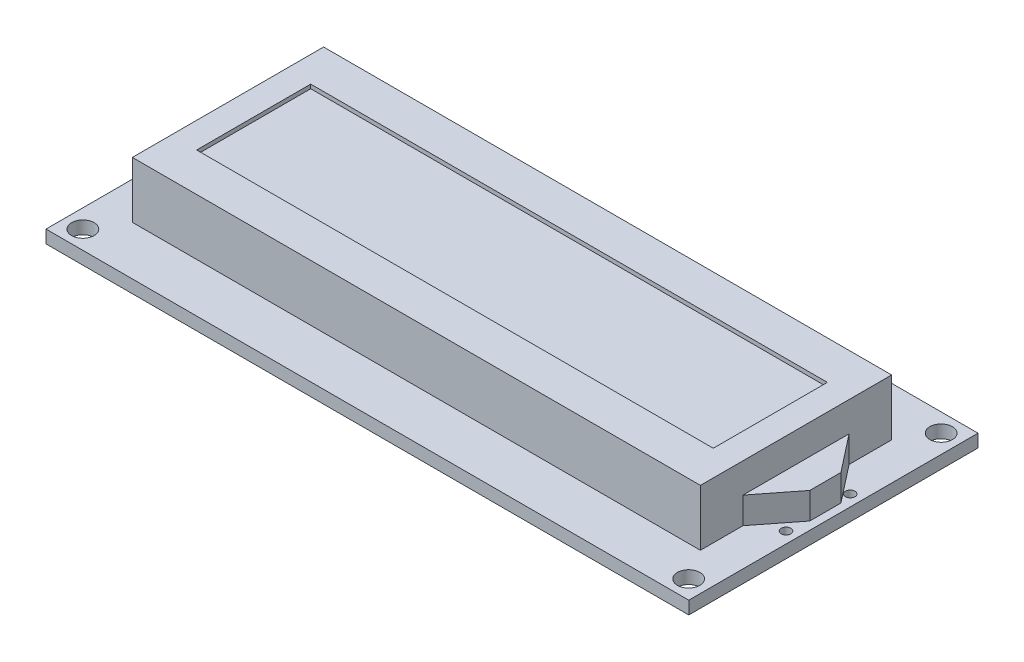
SolidWorks part; units mm, degrees
ref_plane "Front" through (0, 0, 0) normal (0, 0, 1) x (1, 0, 0)
ref_plane "Top" through (0, 0, 0) normal (0, 1, 0) x (1, 0, 0)
ref_plane "Right" through (0, 0, 0) normal (1, 0, 0) x (0, 0, -1)
sketch "Sketch1" plane through (0, 0, 0) normal (0, 1, 0) x (1, 0, 0)
  line L0 (2.3, 2.2882) -> (77.7, 2.2882) construction
  line L1 (0, 0) -> (80, 0)
  line L2 (0, 0) -> (0, 36)
  line L3 (0, 36) -> (80, 36)
  line L4 (80, 0) -> (80, 36)
  line L5 (77.7, 2.2882) -> (77.7, 33.7118) construction
  line L6 (40, -3.9777) -> (40, 42.0163) construction
  line L7 (85.2683, 18) -> (26.439, 18) construction
  circle A0 centre (2.3, 33.7118) radius 1.4
  circle A1 centre (2.3, 2.2882) radius 1.4
  circle A2 centre (77.7, 2.2882) radius 1.4
  circle A3 centre (77.7, 33.7118) radius 1.4
  point P13 (77.7, 18)
  point P14 (80, 18)
  point P19 (40, 0)
  point P20 (40, 2.2882)
  dimension "D3" = 2.8
  dimension "D1" = 80
  dimension "D2" = 36
  dimension "D4" = 31.4236
  dimension "D5" = 75.4
extrude "Boss-Extrude1" add sketch "Sketch1" along normal blind 1.6
sketch "Sketch2" plane through (0, 1.6, 0) normal (0, 1, 0) x (1, 0, 0)
  line L0 (40, 36) -> (40, 0) construction
  line L1 (4.65, 6.1) -> (75.35, 6.1)
  line L2 (4.65, 6.1) -> (4.65, 29.9)
  line L3 (4.65, 29.9) -> (75.35, 29.9)
  line L4 (75.35, 6.1) -> (75.35, 29.9)
  line L5 (4.65, 6.1) -> (75.35, 29.9) construction
  line L6 (4.65, 29.9) -> (75.35, 6.1) construction
  line L7 (80, 36) -> (0, 36) construction
  line L8 (0, 0) -> (80, 0) construction
  line L9 (0, 18) -> (80, 18) construction
  line L10 (0, 36) -> (0, 0) construction
  line L11 (80, 0) -> (80, 36) construction
  point P0 (40, 18)
  dimension "D1" = 70.7
  dimension "D2" = 23.8
extrude "Boss-Extrude2" add sketch "Sketch2" along normal blind 7
sketch "Sketch3" plane through (0, 8.6, 0) normal (0, 1, 0) x (1, 0, 0)
  line L0 (4.65, 29.9) -> (4.65, 6.1) construction
  line L1 (7.85, 25.1) -> (72.15, 25.1)
  line L2 (7.85, 25.1) -> (7.85, 10.9)
  line L3 (7.85, 10.9) -> (72.15, 10.9)
  line L4 (72.15, 25.1) -> (72.15, 10.9)
  line L5 (75.35, 6.1) -> (75.35, 29.9) construction
  line L6 (75.35, 29.9) -> (4.65, 29.9) construction
  line L7 (4.65, 6.1) -> (75.35, 6.1) construction
  dimension "D1" = 3.2
  dimension "D2" = 3.2
  dimension "D3" = 4.8
  dimension "D4" = 4.8
extrude "Cut-Extrude1" cut sketch "Sketch3" against normal blind 0.5
sketch "Sketch4" plane through (0, 1.6, 0) normal (0, 1, 0) x (1, 0, 0)
  line L0 (75.35, 24.6) -> (79, 19.94)
  line L1 (75.35, 6.1) -> (75.35, 29.9) construction
  line L2 (79, 19.94) -> (79, 16.06)
  line L3 (79, 16.06) -> (75.35, 11.4)
  line L4 (75.35, 11.4) -> (75.35, 24.6)
  line L5 (80, 0) -> (80, 36) construction
  dimension "D1" = 5.3
  dimension "D2" = 5.3
  dimension "D3" = 3.88
  dimension "D4" = 1
extrude "Boss-Extrude3" add sketch "Sketch4" along normal blind 3.3
sketch "Sketch5" plane through (0, 1.6, 0) normal (0, 1, 0) x (1, 0, 0)
  line L0 (0, 36) -> (0, 0) construction
  line L2 (80, 36) -> (0, 36) construction
  line L3 (80, 0) -> (80, 36) construction
  line L4 (0, 0) -> (80, 0) construction
  circle A0 centre (7.88, 33.65) radius 0.6
  circle A1 centre (10.42, 33.65) radius 0.6
  circle A2 centre (12.96, 33.65) radius 0.6
  circle A3 centre (15.5, 33.65) radius 0.6
  circle A4 centre (18.04, 33.65) radius 0.6
  circle A5 centre (20.58, 33.65) radius 0.6
  circle A6 centre (23.12, 33.65) radius 0.6
  circle A7 centre (25.66, 33.65) radius 0.6
  circle A8 centre (28.2, 33.65) radius 0.6
  circle A9 centre (30.74, 33.65) radius 0.6
  circle A10 centre (33.28, 33.65) radius 0.6
  circle A11 centre (35.82, 33.65) radius 0.6
  circle A12 centre (38.36, 33.65) radius 0.6
  circle A13 centre (40.9, 33.65) radius 0.6
  circle A14 centre (43.44, 33.65) radius 0.6
  circle A15 centre (45.98, 33.65) radius 0.6
  circle A16 centre (78.6, 21.5) radius 0.6
  circle A17 centre (78.6, 13.5) radius 0.6
  dimension "D1" = 1.2
  dimension "D2" = 7.88
  dimension "D3" = 2.35
  dimension "D5" = 1.4
  dimension "D6" = 14.5
  dimension "D7" = 13.5
  dimension "D8" = 8
  dimension "D4" = 16
extrude "Cut-Extrude2" cut sketch "Sketch5" against normal through all
